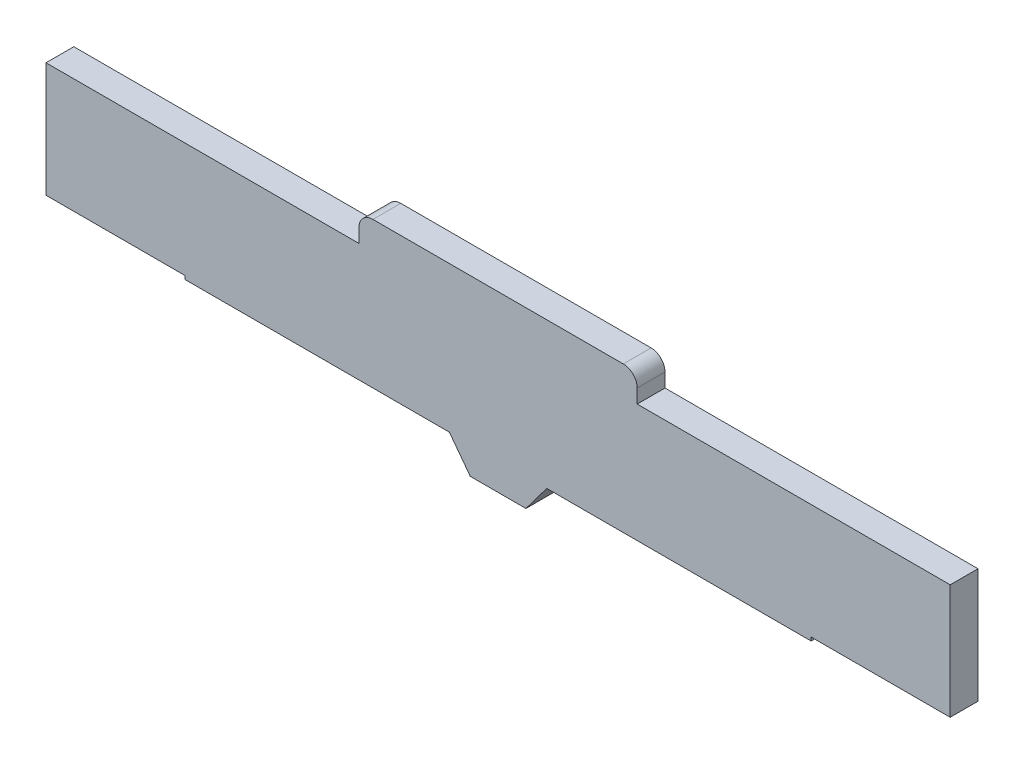
SolidWorks part; units mm, degrees
ref_plane "Front Plane" through (0, 0, 0) normal (0, 0, 1) x (1, 0, 0)
ref_plane "Top Plane" through (0, 0, 0) normal (0, 1, 0) x (1, 0, 0)
ref_plane "Right Plane" through (0, 0, 0) normal (1, 0, 0) x (0, 0, -1)
sketch "Sketch1" plane through (0, 0, 0) normal (0, 0, 1) x (1, 0, 0)
  line L1 (-26.3292, -11.8292) -> (-26.3292, -10.8292)
  line L2 (-6.3292, -11.8292) -> (-6.3292, -10.8292)
  line L3 (-48.8292, -11.8292) -> (-48.8292, -20.0792)
  line L4 (16.1708, -11.8292) -> (16.1708, -20.0792)
  line L5 (-25.3292, -9.8292) -> (-7.3292, -9.8292)
  line L6 (-38.8292, -20.3292) -> (-19.8292, -20.3292)
  line L7 (-19.8292, -20.3292) -> (-18.3292, -22.3292)
  line L8 (-16.3292, -22.3292) -> (-18.3292, -22.3292)
  line L9 (-16.3292, -22.3292) -> (-14.3292, -22.3292)
  line L10 (-48.8292, -20.0792) -> (-38.8292, -20.0792)
  line L11 (-12.8292, -20.3292) -> (-14.3292, -22.3292)
  line L12 (-12.8292, -20.3292) -> (6.1708, -20.3292)
  line L13 (6.1708, -20.0792) -> (16.1708, -20.0792)
  line L16 (-6.3292, -11.8292) -> (16.1708, -11.8292)
  line L19 (16.1708, -12.3292) -> (16.1708, -20.3292) construction
  line L21 (-48.8292, -11.8292) -> (-26.3292, -11.8292)
  line L22 (-38.8292, -20.0792) -> (-38.8292, -20.3292)
  line L23 (6.1708, -20.0792) -> (6.1708, -20.3292)
  line L24 (-48.8292, -12.3292) -> (-48.8292, -20.3292) construction
  line L29 (-38.8292, -12.3292) -> (-38.8292, -20.3292) construction
  line L34 (6.1708, -12.3292) -> (6.1708, -20.3292) construction
  arc A0 (-7.3292, -9.8292) -> (-6.3292, -10.8292) centre (-7.3292, -10.8292) cw
  arc A1 (-25.3292, -9.8292) -> (-26.3292, -10.8292) centre (-25.3292, -10.8292) ccw
  point P0 (-48.8292, -19.8292)
  point P1 (-19.8292, -19.8292)
  point P20 (-12.8292, -19.8292)
  point P21 (16.1708, -19.8292)
  point P23 (-19.8292, -20.3292)
  point P24 (-48.8292, -19.3292)
  point P25 (-19.8292, -19.3292)
  point P26 (-12.8292, -19.3292)
  point P27 (16.1708, -19.3292)
  point P28 (-48.8292, -18.8292)
  point P29 (-19.8292, -18.8292)
  point P30 (-12.8292, -18.8292)
  point P31 (16.1708, -18.8292)
  point P32 (-48.8292, -18.3292)
  point P33 (-19.8292, -18.3292)
  point P34 (-12.8292, -18.3292)
  point P35 (16.1708, -18.3292)
extrude "Boss-Extrude1" add sketch "Sketch1" along normal blind 2
